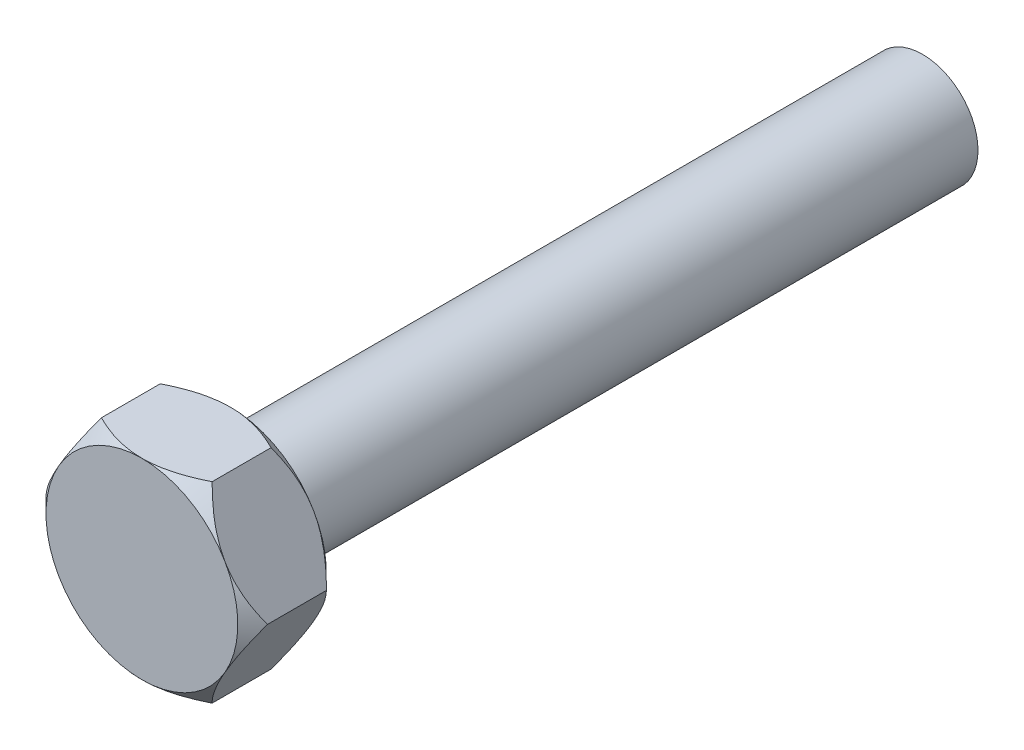
SolidWorks part; units mm, degrees
ref_plane "Front Plane" through (0, 0, 0) normal (0, 0, 1) x (1, 0, 0)
ref_plane "Top Plane" through (0, 0, 0) normal (0, 1, 0) x (1, 0, 0)
ref_plane "Right Plane" through (0, 0, 0) normal (1, 0, 0) x (0, 0, -1)
sketch "Sketch1" plane through (0, 0, 0) normal (0, 0, 1) x (1, 0, 0)
  line L1 (-10, 17.3205) -> (-20, 0)
  line L2 (-20, 0) -> (-10, -17.3205)
  line L3 (-10, -17.3205) -> (10, -17.3205)
  line L4 (10, -17.3205) -> (20, 0)
  line L5 (20, 0) -> (10, 17.3205)
  line L6 (10, 17.3205) -> (-10, 17.3205)
  circle A0 centre (0, 0) radius 17.3205 construction
  dimension "D1" = 30
extrude "Boss-Extrude1" add sketch "Sketch1" along normal mid plane 16
sketch "Sketch2" plane through (0, 0, 8) normal (0, 0, 1) x (1, 0, 0)
  line L0 (-10, 17.3205) -> (-20, 0) construction
  circle A0 centre (0, 0) radius 17.3205
extrude "Cut-Extrude1" cut sketch "Sketch2" against normal through all draft 45 flip side to cut
mirror "Mirror1" about plane through (0, 0, 0) normal (0, 0, 1) of "Cut-Extrude1"
sketch "Sketch3" plane through (0, 0, -8) normal (0, 0, -1) x (-1, 0, 0)
  circle A0 centre (0, 0) radius 10
  dimension "D1" = 20
extrude "Boss-Extrude2" add sketch "Sketch3" along normal blind 125
cosmetic thread "Cosmetic Thread1" parameters "D2"=17.252
